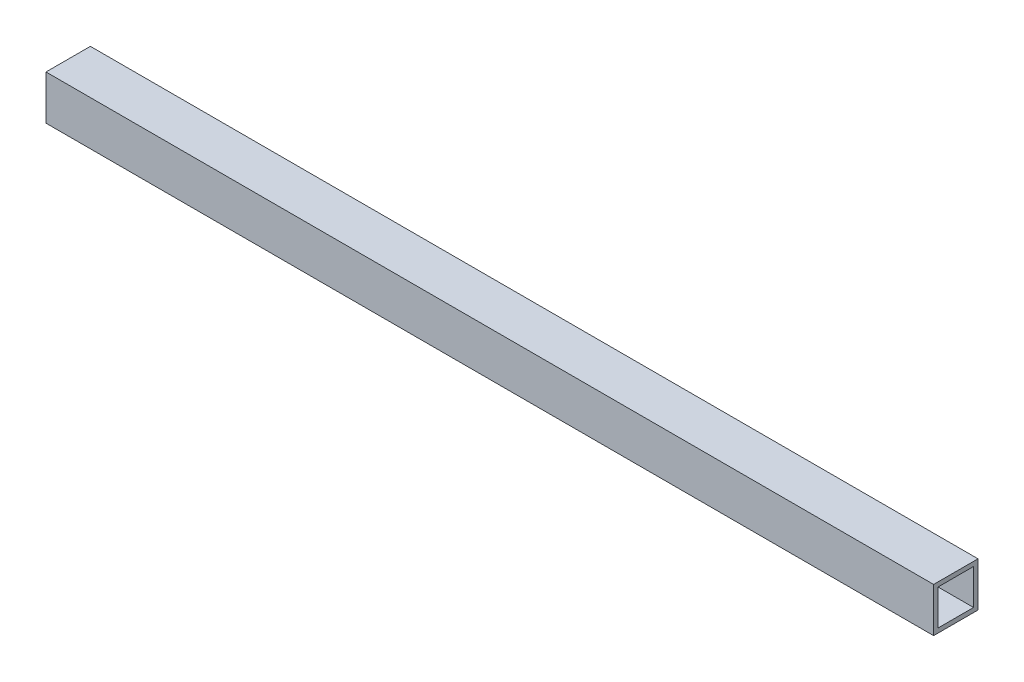
SolidWorks part; units mm, degrees
ref_plane "Front Plane" through (0, 0, 0) normal (0, 0, 1) x (1, 0, 0)
ref_plane "Top Plane" through (0, 0, 0) normal (0, 1, 0) x (1, 0, 0)
ref_plane "Right Plane" through (0, 0, 0) normal (1, 0, 0) x (0, 0, -1)
sketch "Sketch1" plane through (0, 0, 0) normal (1, 0, 0) x (0, 0, -1)
  line L0 (-6, 6) -> (6, 6)
  line L1 (-7.5, 7.5) -> (7.5, 7.5)
  line L2 (-7.5, 7.5) -> (-7.5, -7.5)
  line L3 (-7.5, -7.5) -> (7.5, -7.5)
  line L4 (7.5, 7.5) -> (7.5, -7.5)
  line L5 (-7.5, 7.5) -> (7.5, -7.5) construction
  line L6 (-7.5, -7.5) -> (7.5, 7.5) construction
  line L7 (6, 6) -> (6, -6)
  line L8 (-6, -6) -> (6, -6)
  line L9 (-6, 6) -> (-6, -6)
  point P0 (0, 0)
  dimension "D1" = 15
  dimension "D2" = 15
  dimension "D3" = 1.5
extrude "Boss-Extrude1" add sketch "Sketch1" along normal blind 300
sketch "Sketch2" plane through (0, 7.5, 0) normal (0, 1, 0) x (1, 0, 0)
  line L0 (0, 0) -> (300, 0) construction
  line L1 (300, 7.5) -> (300, -7.5) construction
  circle A0 centre (150, 0) radius 2
  dimension "D1" = 4
extrude "Cut-Extrude1" [suppressed] cut sketch "Sketch2" against normal through all
